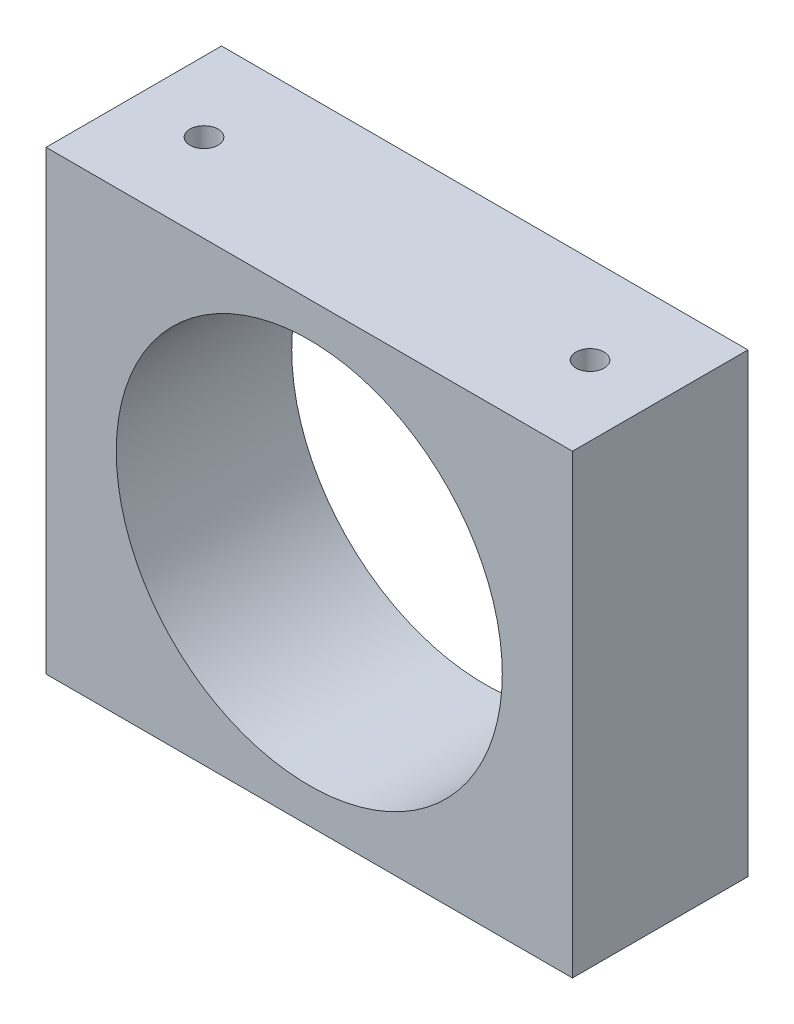
SolidWorks part; units mm, degrees
ref_plane "Plan de face" through (0, 0, 0) normal (0, 0, 1) x (1, 0, 0)
ref_plane "Plan de dessus" through (0, 0, 0) normal (0, 1, 0) x (1, 0, 0)
ref_plane "Plan de droite" through (0, 0, 0) normal (1, 0, 0) x (0, 0, -1)
sketch "Esquisse1" plane through (0, 0, 0) normal (0, 0, 1) x (1, 0, 0)
  line L1 (0, 0) -> (30, 0)
  line L2 (0, 0) -> (0, 26)
  line L3 (0, 26) -> (30, 26)
  line L4 (30, 0) -> (30, 26)
  circle A0 centre (15, 13) radius 11
  dimension "D3" = 22
  dimension "D1" = 26
  dimension "D2" = 30
  dimension "D4" = 15
  dimension "D5" = 13
extrude "Boss.-Extru.1" add sketch "Esquisse1" along normal blind 10
hole_wizard "Trou pour taraudage pour trou taraudé M21" positions "Esquisse2" profile "Esquisse3" hole size "M2" standard "ISO"
sketch "Esquisse2" plane through (0, 26, 0) normal (0, 1, 0) x (1, 0, 0)
  line L0 (0, -10) -> (0, 0) construction
  line L1 (30, -10) -> (30, 0) construction
  line L2 (30, 0) -> (0, 0) construction
  point P0 (4, -5)
  point P2 (26, -5)
  dimension "D1" = 4
  dimension "D2" = 4
  dimension "D3" = 5
  dimension "D4" = 5
sketch "Esquisse3" plane through (4, 26, 5) normal (1, 0, 0) x (0, 0, 1)
  line L0 (0, 0) -> (0, 5.4807)
  line L1 (0, 5.4807) -> (0.8, 5)
  line L2 (0.8, 5) -> (0.8, 0)
  line L5 (0.8, 0) -> (0, 0)
  line L10 (0, 5.4807) -> (-0.8, 5) construction
  line L11 (0, -6.35) -> (0, 107.95) construction
  dimension "Diamètre du perçage" = 1.6
  dimension "Profondeur du perçage" = 5
  dimension "Angle de pointe" = 118
hole_wizard "Trou pour taraudage pour trou taraudé M22" positions "Esquisse4" profile "Esquisse5" hole size "M2" standard "ISO"
sketch "Esquisse4" plane through (0, 0, 0) normal (0, -1, 0) x (-1, 0, 0)
  line L0 (-30, -10) -> (-30, 0) construction
  line L1 (0, -10) -> (0, 0) construction
  line L2 (0, 0) -> (-30, 0) construction
  point P0 (-4, -5)
  point P2 (-26, -5)
  dimension "D1" = 4
  dimension "D2" = 4
  dimension "D3" = 5
  dimension "D4" = 5
sketch "Esquisse5" plane through (4, 0, 5) normal (1, 0, 0) x (0, 0, -1)
  line L0 (0, 0) -> (0, 5.4807)
  line L1 (0, 5.4807) -> (0.8, 5)
  line L2 (0.8, 5) -> (0.8, 0)
  line L5 (0.8, 0) -> (0, 0)
  line L10 (0, 5.4807) -> (-0.8, 5) construction
  line L11 (0, -6.35) -> (0, 107.95) construction
  dimension "Diamètre du perçage" = 1.6
  dimension "Profondeur du perçage" = 5
  dimension "Angle de pointe" = 118
equation "\"D4@Esquisse1\"=\"D2@Esquisse1\"/2"
equation "\"D5@Esquisse1\"=\"D1@Esquisse1\"/2"
equation "\"D3@Esquisse2\"=\"D1@Boss.-Extru.1\"/2"
equation "\"D4@Esquisse2\"=\"D1@Boss.-Extru.1\"/2"
equation "\"D3@Esquisse4\"=\"D1@Boss.-Extru.1\"/2"
equation "\"D4@Esquisse4\"=\"D1@Boss.-Extru.1\"/2"
